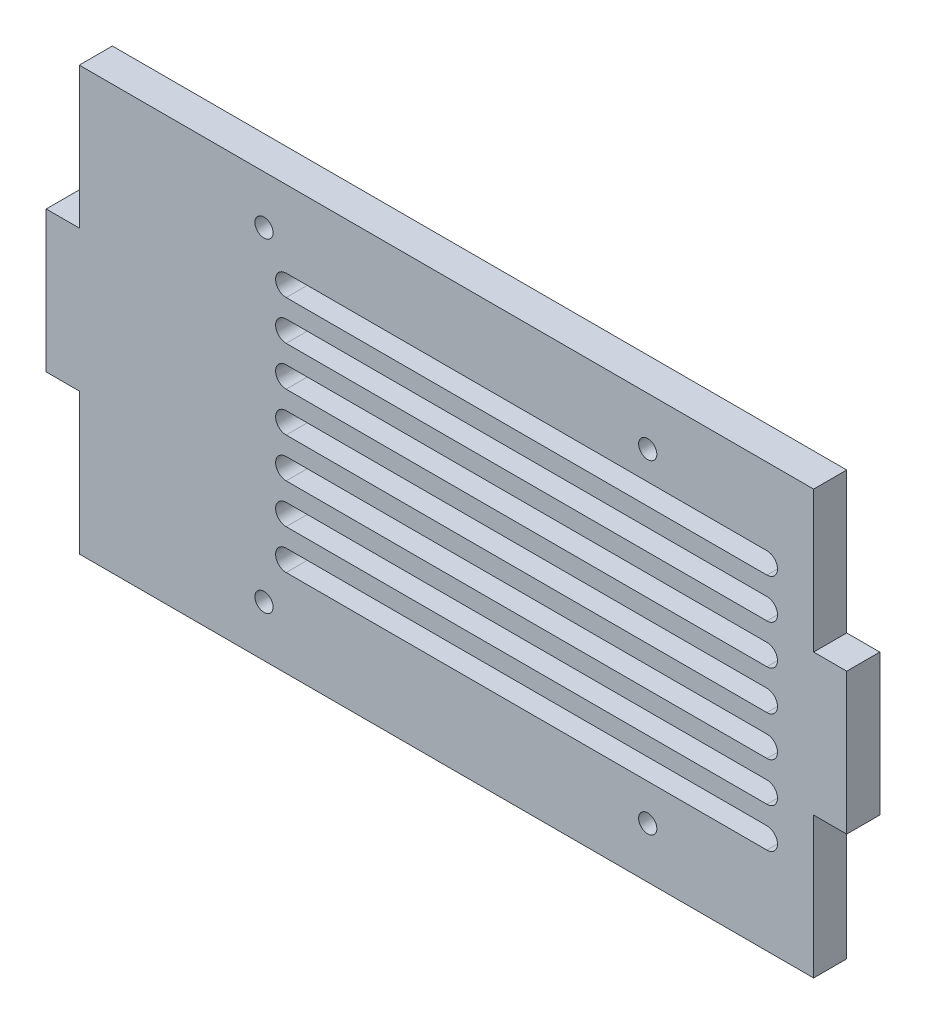
SolidWorks part; units mm, degrees
ref_plane "Alzado" through (0, 0, 0) normal (0, 0, 1) x (1, 0, 0)
ref_plane "Planta" through (0, 0, 0) normal (0, 1, 0) x (1, 0, 0)
ref_plane "Vista lateral" through (0, 0, 0) normal (1, 0, 0) x (0, 0, -1)
sketch "Croquis1" plane through (0, 0, 0) normal (0, 0, 1) x (1, 0, 0)
  line L9 (63.4201, -35.8034) -> (38.3201, -35.8034)
  line L10 (-43, 24) -> (68, 24)
  line L11 (-43, 24) -> (-43, -40)
  line L12 (-43, -40) -> (68, -40)
  line L13 (68, 24) -> (68, -40)
  line L14 (50.7201, 10.8079) -> (50.8201, 10.8079)
  line L15 (66.3781, 17.6966) -> (66.3781, -33.3034)
  line L16 (50.8201, 12.4739) -> (50.7201, 12.4739)
  line L17 (63.4201, 20.1966) -> (-15.5799, 20.1966)
  line L18 (-18.5799, 17.1966) -> (-18.5799, -32.8034)
  line L19 (-15.5799, -35.8034) -> (-11.7299, -35.8034)
  line L20 (-8.545, -31.0034) -> (-8.545, -31.1034)
  line L21 (-11.6299, -35.8034) -> (-4.3299, -35.8034)
  line L22 (-7.6536, -31.1034) -> (-7.6536, -31.0034)
  line L23 (-4.2299, -35.8034) -> (6.1701, -35.8034)
  line L24 (12.9043, -25.3034) -> (12.9043, -25.4034)
  line L25 (6.2701, -35.8034) -> (20.5701, -35.8034)
  line L26 (14.2352, -25.4034) -> (14.2352, -25.3034)
  line L27 (20.6701, -35.8034) -> (31.4201, -35.8034)
  line L28 (33.7192, -23.3034) -> (33.7192, -23.4034)
  line L29 (31.5201, -35.8034) -> (38.3201, -35.8034)
  line L30 (47.1201, -25.5534) -> (47.2201, -25.5534)
  line L31 (60.9393, 10.8079) -> (-11.7299, 10.8079) construction
  line L32 (47.2201, -24.3034) -> (47.1201, -24.3034)
  line L33 (60.9393, 9.2127) -> (-11.7299, 9.2127)
  line L34 (50.7201, -7.3962) -> (50.8201, -7.3962)
  line L35 (60.9393, 12.4032) -> (-11.7299, 12.4032)
  line L36 (50.8201, -5.2506) -> (50.7201, -5.2506)
  line L37 (60.9393, 4.8079) -> (-11.7299, 4.8079) construction
  line L38 (60.9393, 3.2127) -> (-11.7299, 3.2127)
  line L39 (60.9393, 6.4032) -> (-11.7299, 6.4032)
  line L40 (60.9393, -1.1921) -> (-11.7299, -1.1921) construction
  line L41 (60.9393, -2.7873) -> (-11.7299, -2.7873)
  line L42 (60.9393, 0.4032) -> (-11.7299, 0.4032)
  line L43 (60.9393, -7.1921) -> (-11.7299, -7.1921) construction
  line L44 (60.9393, -8.7873) -> (-11.7299, -8.7873)
  line L45 (60.9393, -5.5968) -> (-11.7299, -5.5968)
  line L46 (60.9393, -13.1921) -> (-11.7299, -13.1921) construction
  line L47 (60.9393, -14.7873) -> (-11.7299, -14.7873)
  line L48 (60.9393, -11.5968) -> (-11.7299, -11.5968)
  line L49 (60.9393, -19.1921) -> (-11.7299, -19.1921) construction
  line L50 (60.9393, -20.7873) -> (-11.7299, -20.7873)
  line L51 (60.9393, -17.5968) -> (-11.7299, -17.5968)
  line L52 (60.9393, -25.1921) -> (-11.7299, -25.1921) construction
  line L53 (60.9393, -26.7873) -> (-11.7299, -26.7873)
  line L54 (60.9393, -23.5968) -> (-11.7299, -23.5968)
  circle A39 centre (42.9201, -32.3034) radius 1.375
  circle A40 centre (42.9201, 16.6966) radius 1.375
  arc A42 (66.3781, 17.6966) -> (63.4201, 20.1966) centre (63.4201, 17.1966) ccw
  arc A43 (-15.5799, 20.1966) -> (-18.5799, 17.1966) centre (-15.5799, 17.1966) ccw
  arc A44 (-18.5799, -32.8034) -> (-15.5799, -35.8034) centre (-15.5799, -32.8034) ccw
  arc A45 (63.4201, -35.8034) -> (66.3781, -33.3034) centre (63.4201, -32.8034) ccw
  circle A47 centre (-15.0799, -32.3034) radius 1.375
  circle A48 centre (-15.0799, 16.6966) radius 1.375
  arc A65 (60.9393, 9.2127) -> (60.9393, 12.4032) centre (60.9393, 10.8079) ccw
  arc A66 (-11.7299, 12.4032) -> (-11.7299, 9.2127) centre (-11.7299, 10.8079) ccw
  arc A67 (60.9393, 3.2127) -> (60.9393, 6.4032) centre (60.9393, 4.8079) ccw
  arc A68 (-11.7299, 6.4032) -> (-11.7299, 3.2127) centre (-11.7299, 4.8079) ccw
  arc A69 (60.9393, -2.7873) -> (60.9393, 0.4032) centre (60.9393, -1.1921) ccw
  arc A70 (-11.7299, 0.4032) -> (-11.7299, -2.7873) centre (-11.7299, -1.1921) ccw
  arc A71 (60.9393, -8.7873) -> (60.9393, -5.5968) centre (60.9393, -7.1921) ccw
  arc A72 (-11.7299, -5.5968) -> (-11.7299, -8.7873) centre (-11.7299, -7.1921) ccw
  arc A73 (60.9393, -14.7873) -> (60.9393, -11.5968) centre (60.9393, -13.1921) ccw
  arc A74 (-11.7299, -11.5968) -> (-11.7299, -14.7873) centre (-11.7299, -13.1921) ccw
  arc A75 (60.9393, -20.7873) -> (60.9393, -17.5968) centre (60.9393, -19.1921) ccw
  arc A76 (-11.7299, -17.5968) -> (-11.7299, -20.7873) centre (-11.7299, -19.1921) ccw
  arc A77 (60.9393, -26.7873) -> (60.9393, -23.5968) centre (60.9393, -25.1921) ccw
  arc A78 (-11.7299, -23.5968) -> (-11.7299, -26.7873) centre (-11.7299, -25.1921) ccw
  point P5 (24.6047, 10.8079)
  point P53 (24.6047, 4.8079)
  point P75 (24.6047, -1.1921)
  point P82 (24.6047, -7.1921)
  point P89 (24.6047, -13.1921)
  point P96 (24.6047, -19.1921)
  point P103 (24.6047, -25.1921)
  dimension "D2" = 43
  dimension "D3" = 24
  dimension "D4" = 7
  dimension "D17" = 111
  dimension "D19" = 64
extrude "Saliente-Extruir1" add sketch "Croquis1" along normal blind 5
sketch "Croquis2" plane through (68, 0, 0) normal (1, 0, 0) x (0, 0, -1)
  line L0 (-5, 24) -> (-5, -40) construction
  line L1 (-5, 2.6667) -> (0, 2.6667)
  line L2 (-5, 2.6667) -> (-5, -18.6667)
  line L3 (-5, -18.6667) -> (0, -18.6667)
  line L4 (0, 2.6667) -> (0, -18.6667)
  line L5 (0, 24) -> (0, -40) construction
  line L6 (-5, 24) -> (0, 24) construction
  dimension "D1" = 21.3333
  dimension "D2" = 21.3333
extrude "Saliente-Extruir2" add sketch "Croquis2" along normal blind 5
sketch "Croquis3" plane through (-43, 0, 0) normal (-1, 0, 0) x (0, 0, 1)
  line L0 (0, 24) -> (0, -40) construction
  line L1 (0, 2.6667) -> (5, 2.6667)
  line L2 (0, 2.6667) -> (0, -18.6667)
  line L3 (0, -18.6667) -> (5, -18.6667)
  line L4 (5, 2.6667) -> (5, -18.6667)
  line L5 (5, 24) -> (5, -40) construction
  line L6 (5, 24) -> (0, 24) construction
  dimension "D1" = 21.3333
  dimension "D2" = 21.3333
extrude "Saliente-Extruir3" add sketch "Croquis3" along normal blind 5
sketch "Croquis4" plane through (0, 0, 0) normal (0, 0, -1) x (-1, 0, 0)
  line L0 (-60.9393, 12.4032) -> (11.7299, 12.4032) construction
  line L1 (-60.9393, 9.2127) -> (11.7299, 9.2127) construction
  line L2 (-60.9393, 6.4032) -> (11.7299, 6.4032) construction
  line L3 (-60.9393, 3.2127) -> (11.7299, 3.2127) construction
  line L4 (-60.9393, 0.4032) -> (11.7299, 0.4032) construction
  line L5 (-60.9393, -2.7873) -> (11.7299, -2.7873) construction
  line L6 (-60.9393, -5.5968) -> (11.7299, -5.5968) construction
  line L7 (-60.9393, -8.7873) -> (11.7299, -8.7873) construction
  line L8 (-60.9393, -11.5968) -> (11.7299, -11.5968) construction
  line L9 (-60.9393, -14.7873) -> (11.7299, -14.7873) construction
  line L10 (-60.9393, -17.5968) -> (11.7299, -17.5968) construction
  line L11 (-60.9393, -20.7873) -> (11.7299, -20.7873) construction
  line L12 (-68, 24) -> (-68, 2.6667)
  line L13 (-68, 2.6667) -> (-73, 2.6667)
  line L14 (-73, 2.6667) -> (-73, -18.6667)
  line L15 (-73, -18.6667) -> (-68, -18.6667)
  line L16 (-68, -18.6667) -> (-68, -40)
  line L17 (-68, -40) -> (43, -40)
  line L18 (43, -40) -> (43, -18.6667)
  line L19 (43, -18.6667) -> (48, -18.6667)
  line L20 (48, -18.6667) -> (48, 2.6667)
  line L21 (48, 2.6667) -> (43, 2.6667)
  line L22 (43, 2.6667) -> (43, 24)
  line L23 (43, 24) -> (-68, 24)
  line L24 (-68, 24) -> (-68, 2.6667)
  line L25 (-68, 2.6667) -> (-73, 2.6667)
  line L26 (-73, 2.6667) -> (-73, -18.6667)
  line L27 (-73, -18.6667) -> (-68, -18.6667)
  line L28 (-68, -18.6667) -> (-68, -40)
  line L29 (-68, -40) -> (43, -40)
  line L30 (43, -40) -> (43, -18.6667)
  line L31 (43, -18.6667) -> (48, -18.6667)
  line L32 (48, -18.6667) -> (48, 2.6667)
  line L33 (48, 2.6667) -> (43, 2.6667)
  line L34 (43, 2.6667) -> (43, 24)
  line L35 (43, 24) -> (-68, 24)
  line L36 (-60.9393, -23.5968) -> (11.7299, -23.5968) construction
  line L37 (-60.9393, -26.7873) -> (11.7299, -26.7873) construction
  line L38 (-60.9393, 12.4032) -> (11.7299, 12.4032)
  line L39 (-60.9393, 9.2127) -> (11.7299, 9.2127)
  line L40 (-60.9393, 6.4032) -> (11.7299, 6.4032)
  line L41 (-60.9393, 3.2127) -> (11.7299, 3.2127)
  line L42 (-60.9393, 0.4032) -> (11.7299, 0.4032)
  line L43 (-60.9393, -2.7873) -> (11.7299, -2.7873)
  line L44 (-60.9393, -5.5968) -> (11.7299, -5.5968)
  line L45 (-60.9393, -8.7873) -> (11.7299, -8.7873)
  line L46 (-60.9393, -11.5968) -> (11.7299, -11.5968)
  line L47 (-60.9393, -14.7873) -> (11.7299, -14.7873)
  line L48 (-60.9393, -17.5968) -> (11.7299, -17.5968)
  line L49 (-60.9393, -20.7873) -> (11.7299, -20.7873)
  line L50 (-60.9393, -23.5968) -> (11.7299, -23.5968)
  line L51 (-60.9393, -26.7873) -> (11.7299, -26.7873)
  arc A0 (11.7299, 9.2127) -> (11.7299, 12.4032) centre (11.7299, 10.8079) ccw construction
  arc A1 (11.7299, 3.2127) -> (11.7299, 6.4032) centre (11.7299, 4.8079) ccw construction
  arc A2 (11.7299, -2.7873) -> (11.7299, 0.4032) centre (11.7299, -1.1921) ccw construction
  arc A3 (11.7299, -8.7873) -> (11.7299, -5.5968) centre (11.7299, -7.1921) ccw construction
  arc A4 (11.7299, -14.7873) -> (11.7299, -11.5968) centre (11.7299, -13.1921) ccw construction
  arc A5 (11.7299, -20.7873) -> (11.7299, -17.5968) centre (11.7299, -19.1921) ccw construction
  arc A6 (11.7299, -26.7873) -> (11.7299, -23.5968) centre (11.7299, -25.1921) ccw construction
  arc A7 (-60.9393, -23.5968) -> (-60.9393, -26.7873) centre (-60.9393, -25.1921) ccw construction
  arc A8 (-60.9393, -17.5968) -> (-60.9393, -20.7873) centre (-60.9393, -19.1921) ccw construction
  arc A9 (-60.9393, -11.5968) -> (-60.9393, -14.7873) centre (-60.9393, -13.1921) ccw construction
  arc A10 (-60.9393, -5.5968) -> (-60.9393, -8.7873) centre (-60.9393, -7.1921) ccw construction
  arc A11 (-60.9393, 0.4032) -> (-60.9393, -2.7873) centre (-60.9393, -1.1921) ccw construction
  arc A12 (-60.9393, 6.4032) -> (-60.9393, 3.2127) centre (-60.9393, 4.8079) ccw construction
  arc A13 (-60.9393, 12.4032) -> (-60.9393, 9.2127) centre (-60.9393, 10.8079) ccw construction
  circle A14 centre (-42.9201, -32.3034) radius 1.375 construction
  circle A15 centre (15.0799, -32.3034) radius 1.375 construction
  circle A16 centre (15.0799, 16.6966) radius 1.375 construction
  circle A17 centre (-42.9201, 16.6966) radius 1.375 construction
  arc A18 (11.7299, 9.2127) -> (11.7299, 12.4032) centre (11.7299, 10.8079) ccw
  arc A19 (11.7299, 3.2127) -> (11.7299, 6.4032) centre (11.7299, 4.8079) ccw
  arc A20 (11.7299, -2.7873) -> (11.7299, 0.4032) centre (11.7299, -1.1921) ccw
  arc A21 (11.7299, -8.7873) -> (11.7299, -5.5968) centre (11.7299, -7.1921) ccw
  arc A22 (11.7299, -14.7873) -> (11.7299, -11.5968) centre (11.7299, -13.1921) ccw
  arc A23 (11.7299, -20.7873) -> (11.7299, -17.5968) centre (11.7299, -19.1921) ccw
  arc A24 (11.7299, -26.7873) -> (11.7299, -23.5968) centre (11.7299, -25.1921) ccw
  arc A25 (-60.9393, -23.5968) -> (-60.9393, -26.7873) centre (-60.9393, -25.1921) ccw
  arc A26 (-60.9393, -17.5968) -> (-60.9393, -20.7873) centre (-60.9393, -19.1921) ccw
  arc A27 (-60.9393, -11.5968) -> (-60.9393, -14.7873) centre (-60.9393, -13.1921) ccw
  arc A28 (-60.9393, -5.5968) -> (-60.9393, -8.7873) centre (-60.9393, -7.1921) ccw
  arc A29 (-60.9393, 0.4032) -> (-60.9393, -2.7873) centre (-60.9393, -1.1921) ccw
  arc A30 (-60.9393, 6.4032) -> (-60.9393, 3.2127) centre (-60.9393, 4.8079) ccw
  arc A31 (-60.9393, 12.4032) -> (-60.9393, 9.2127) centre (-60.9393, 10.8079) ccw
  circle A32 centre (-42.9201, -32.3034) radius 1.375
  circle A33 centre (15.0799, -32.3034) radius 1.375
  circle A34 centre (15.0799, 16.6966) radius 1.375
  circle A35 centre (-42.9201, 16.6966) radius 1.375
  dimension "D1" = 0
